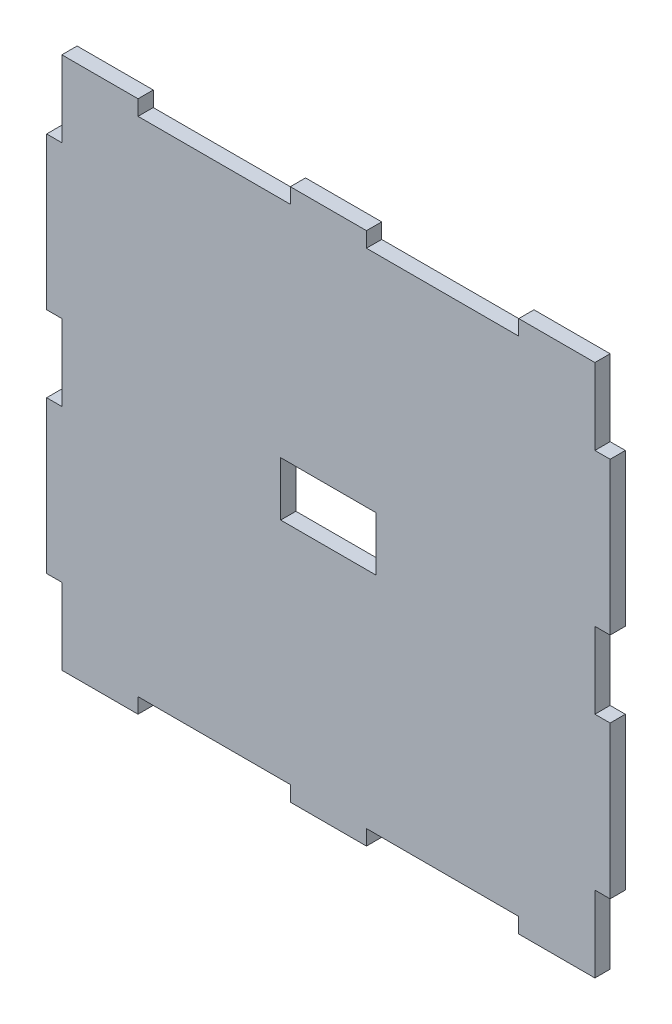
SolidWorks part; units mm, degrees
ref_plane "Front Plane" through (0, 0, 0) normal (0, 0, 1) x (1, 0, 0)
ref_plane "Top Plane" through (0, 0, 0) normal (0, 1, 0) x (1, 0, 0)
ref_plane "Right Plane" through (0, 0, 0) normal (1, 0, 0) x (0, 0, -1)
sketch "Sketch1" plane through (0, 0, 0) normal (0, 0, 1) x (1, 0, 0)
  line L1 (-35, -35) -> (35, -35)
  line L2 (-35, -35) -> (-35, 35)
  line L3 (-35, 35) -> (35, 35)
  line L4 (35, -35) -> (35, 35)
  line L5 (0, 35) -> (0, -35) construction
  line L6 (-35, 0) -> (35, 0) construction
  line L11 (0, 18) -> (0, -18) construction
  line L12 (-17.25, 0) -> (17.25, 0) construction
  point P0 (0, 0)
  point P4 (0, 0)
  dimension "D1" = 70
  dimension "D2" = 70
extrude "Boss-Extrude1" add sketch "Sketch1" against normal blind 2
sketch "Sketch2" plane through (0, 0, 0) normal (0, 0, 1) x (1, 0, 0)
  line L0 (-35, 35) -> (-25, 35)
  line L1 (35, 35) -> (-35, 35) construction
  line L2 (-25, 35) -> (-5, 35)
  line L3 (-5, 35) -> (5, 35)
  line L4 (5, 35) -> (25, 35)
  line L6 (35, 35) -> (35, 25)
  line L7 (-25, 33) -> (-5, 33)
  line L8 (-25, 33) -> (-25, 37)
  line L9 (-25, 37) -> (-5, 37)
  line L10 (-5, 33) -> (-5, 37)
  line L11 (-15, 37) -> (-15, 33) construction
  line L12 (-25, 35) -> (-5, 35) construction
  line L13 (5, 33) -> (25, 33)
  line L14 (5, 33) -> (5, 37)
  line L15 (5, 37) -> (25, 37)
  line L16 (25, 33) -> (25, 37)
  line L17 (15, 37) -> (15, 33) construction
  line L18 (5, 35) -> (25, 35) construction
  line L19 (35, -35) -> (35, 35) construction
  line L20 (35, 25) -> (35, 5)
  line L21 (35, 5) -> (35, -5)
  line L22 (35, -5) -> (35, -25)
  line L23 (-35, -35) -> (-25, -35)
  line L24 (35, -5) -> (33, -5)
  line L25 (35, -5) -> (35, -25)
  line L26 (35, -25) -> (33, -25)
  line L27 (33, -5) -> (33, -25)
  line L28 (35, 25) -> (33, 25)
  line L29 (35, 25) -> (35, 5)
  line L30 (35, 5) -> (33, 5)
  line L31 (33, 25) -> (33, 5)
  line L32 (-35, -35) -> (35, -35) construction
  line L33 (-25, -35) -> (-5, -35)
  line L34 (-5, -35) -> (5, -35)
  line L35 (5, -35) -> (25, -35)
  line L36 (-35, 35) -> (-35, 25)
  line L37 (-25, -35) -> (-5, -35)
  line L38 (-25, -35) -> (-25, -33)
  line L39 (-25, -33) -> (-5, -33)
  line L40 (-5, -35) -> (-5, -33)
  line L41 (5, -35) -> (25, -35)
  line L42 (5, -35) -> (5, -33)
  line L43 (5, -33) -> (25, -33)
  line L44 (25, -35) -> (25, -33)
  line L45 (-35, 35) -> (-35, -35) construction
  line L46 (-35, 25) -> (-35, 5)
  line L47 (-35, 5) -> (-35, -5)
  line L48 (-35, -5) -> (-35, -25)
  line L49 (-35, 25) -> (-37, 25)
  line L50 (-35, 25) -> (-33, 25)
  line L51 (-35, 25) -> (-35, 5)
  line L52 (-35, 5) -> (-33, 5)
  line L53 (-33, 25) -> (-33, 5)
  line L54 (-35, -5) -> (-33, -5)
  line L55 (-35, -5) -> (-35, -25)
  line L56 (-35, -25) -> (-33, -25)
  line L57 (-33, -5) -> (-33, -25)
  line L58 (-35, 25) -> (-35, 5)
  line L59 (-35, 5) -> (-37, 5)
  line L60 (-37, 25) -> (-37, 5)
  line L61 (-35, -5) -> (-37, -5)
  line L62 (-35, -5) -> (-35, -25)
  line L63 (-35, -25) -> (-37, -25)
  line L64 (-37, -5) -> (-37, -25)
  line L65 (-25, -35) -> (-5, -35)
  line L66 (-25, -35) -> (-25, -37)
  line L67 (-25, -37) -> (-5, -37)
  line L68 (-5, -35) -> (-5, -37)
  line L69 (5, -35) -> (25, -35)
  line L70 (5, -35) -> (5, -37)
  line L71 (5, -37) -> (25, -37)
  line L72 (25, -35) -> (25, -37)
  line L73 (35, -25) -> (37, -25)
  line L74 (35, -25) -> (35, -5)
  line L75 (35, -5) -> (37, -5)
  line L76 (37, -25) -> (37, -5)
  line L77 (35, 5) -> (37, 5)
  line L78 (35, 5) -> (35, 25)
  line L79 (35, 25) -> (37, 25)
  line L80 (37, 5) -> (37, 25)
  point P7 (15, 35)
  point P9 (-15, 35)
  point P10 (-15, 35)
  point P14 (15, 35)
  line M25 (35, -35) -> (35, 35)
  line M27 (-35, 35) -> (-35, -35)
  dimension "D1" = 10
  dimension "D2" = 20
  dimension "D3" = 10
  dimension "D4" = 20
  dimension "D5" = 4
  dimension "D6" = 20
  dimension "D7" = 20
  dimension "D8" = 4
  dimension "D9" = 10
  dimension "D10" = 20
  dimension "D11" = 10
  dimension "D12" = 20
  dimension "D13" = 2
  dimension "D14" = 2
  dimension "D15" = 10
  dimension "D16" = 20
  dimension "D17" = 10
  dimension "D18" = 20
  dimension "D19" = 20
  dimension "D20" = 20
  dimension "D21" = 2
  dimension "D22" = 2
  dimension "D23" = 10
  dimension "D24" = 20
  dimension "D25" = 10
  dimension "D26" = 20
  dimension "D27" = 2
  dimension "D28" = 2
  dimension "D29" = 2
  dimension "D30" = 2
  dimension "D31" = 2
  dimension "D32" = 2
  dimension "D33" = 2
  dimension "D34" = 2
sketch "Sketch3" plane through (0, 0, 0) normal (0, 0, 1) x (1, 0, 0)
  line L0 (-35, 35) -> (-25, 35)
  line L2 (-25, 35) -> (-5, 35)
  line L3 (-5, 35) -> (5, 35)
  line L4 (5, 35) -> (25, 35)
  line L6 (35, 35) -> (35, 25)
  line L7 (-25, 33) -> (-5, 33)
  line L8 (-25, 33) -> (-25, 37)
  line L9 (-25, 37) -> (-5, 37)
  line L10 (-5, 33) -> (-5, 37)
  line L11 (-15, 37) -> (-15, 33) construction
  line L12 (-25, 35) -> (-5, 35) construction
  line L13 (5, 33) -> (25, 33)
  line L14 (5, 33) -> (5, 37)
  line L15 (5, 37) -> (25, 37)
  line L16 (25, 33) -> (25, 37)
  line L17 (15, 37) -> (15, 33) construction
  line L18 (5, 35) -> (25, 35) construction
  line L20 (35, 25) -> (35, 5)
  line L21 (35, 5) -> (35, -5)
  line L22 (35, -5) -> (35, -25)
  line L23 (-35, -35) -> (-25, -35)
  line L24 (35, -5) -> (33, -5)
  line L25 (35, -5) -> (35, -25)
  line L26 (35, -25) -> (33, -25)
  line L27 (33, -5) -> (33, -25)
  line L28 (35, 25) -> (33, 25)
  line L29 (35, 25) -> (35, 5)
  line L30 (35, 5) -> (33, 5)
  line L31 (33, 25) -> (33, 5)
  line L33 (-25, -35) -> (-5, -35)
  line L34 (-5, -35) -> (5, -35)
  line L35 (5, -35) -> (25, -35)
  line L36 (-35, 35) -> (-35, 25)
  line L37 (-25, -35) -> (-5, -35)
  line L38 (-25, -35) -> (-25, -33)
  line L39 (-25, -33) -> (-5, -33)
  line L40 (-5, -35) -> (-5, -33)
  line L41 (5, -35) -> (25, -35)
  line L42 (5, -35) -> (5, -33)
  line L43 (5, -33) -> (25, -33)
  line L44 (25, -35) -> (25, -33)
  line L46 (-35, 25) -> (-35, 5)
  line L47 (-35, 5) -> (-35, -5)
  line L48 (-35, -5) -> (-35, -25)
  line L49 (-35, 25) -> (-37, 25)
  line L50 (-35, 25) -> (-33, 25)
  line L51 (-35, 25) -> (-35, 5)
  line L52 (-35, 5) -> (-33, 5)
  line L53 (-33, 25) -> (-33, 5)
  line L54 (-35, -5) -> (-33, -5)
  line L55 (-35, -5) -> (-35, -25)
  line L56 (-35, -25) -> (-33, -25)
  line L57 (-33, -5) -> (-33, -25)
  line L58 (-35, 25) -> (-35, 5)
  line L59 (-35, 5) -> (-37, 5)
  line L60 (-37, 25) -> (-37, 5)
  line L61 (-35, -5) -> (-37, -5)
  line L62 (-35, -5) -> (-35, -25)
  line L63 (-35, -25) -> (-37, -25)
  line L64 (-37, -5) -> (-37, -25)
  line L65 (-25, -35) -> (-5, -35)
  line L66 (-25, -35) -> (-25, -37)
  line L67 (-25, -37) -> (-5, -37)
  line L68 (-5, -35) -> (-5, -37)
  line L69 (5, -35) -> (25, -35)
  line L70 (5, -35) -> (5, -37)
  line L71 (5, -37) -> (25, -37)
  line L72 (25, -35) -> (25, -37)
  line L73 (35, -25) -> (37, -25)
  line L74 (35, -25) -> (35, -5)
  line L75 (35, -5) -> (37, -5)
  line L76 (37, -25) -> (37, -5)
  line L77 (35, 5) -> (37, 5)
  line L78 (35, 5) -> (35, 25)
  line L79 (35, 25) -> (37, 25)
  line L80 (37, 5) -> (37, 25)
  point P7 (15, 35)
  point P9 (-15, 35)
  point P10 (-15, 35)
  point P14 (15, 35)
  dimension "D1" = 10
  dimension "D2" = 20
  dimension "D3" = 10
  dimension "D4" = 20
  dimension "D5" = 4
  dimension "D6" = 20
  dimension "D7" = 20
  dimension "D8" = 4
  dimension "D9" = 10
  dimension "D10" = 20
  dimension "D11" = 10
  dimension "D12" = 20
  dimension "D13" = 2
  dimension "D14" = 2
  dimension "D15" = 10
  dimension "D16" = 20
  dimension "D17" = 10
  dimension "D18" = 20
  dimension "D19" = 20
  dimension "D20" = 20
  dimension "D21" = 2
  dimension "D22" = 2
  dimension "D23" = 10
  dimension "D24" = 20
  dimension "D25" = 10
  dimension "D26" = 20
  dimension "D27" = 2
  dimension "D28" = 2
  dimension "D29" = 2
  dimension "D30" = 2
  dimension "D31" = 2
  dimension "D32" = 2
  dimension "D33" = 2
  dimension "D34" = 2
extrude "Boss-Extrude2" add sketch "Sketch2" against normal blind 2 contours L49 L60 L59 M27 | L61 L64 L63 M27 | L73 L76 L75 M25 | L77 L80 L79 M25
extrude "Cut-Extrude1" cut sketch "Sketch3" against normal blind 2 contours L7 L10 L2 L8 | L13 L16 L4 L14 | L33 L40 L39 L38 | L35 L44 L43 L42
sketch "Sketch4" plane through (0, 0, 0) normal (0, 0, 1) x (1, 0, 0)
  line L1 (-6.265, -3.55) -> (6.265, -3.55)
  line L2 (-6.265, -3.55) -> (-6.265, 3.55)
  line L3 (-6.265, 3.55) -> (6.265, 3.55)
  line L4 (6.265, -3.55) -> (6.265, 3.55)
  line L5 (0, 3.55) -> (0, -3.55) construction
  line L6 (-6.265, 0) -> (6.265, 0) construction
  point P0 (0, 0)
  dimension "D1" = 12.53
  dimension "D2" = 7.1
extrude "Cut-Extrude2" cut sketch "Sketch4" against normal blind 10
